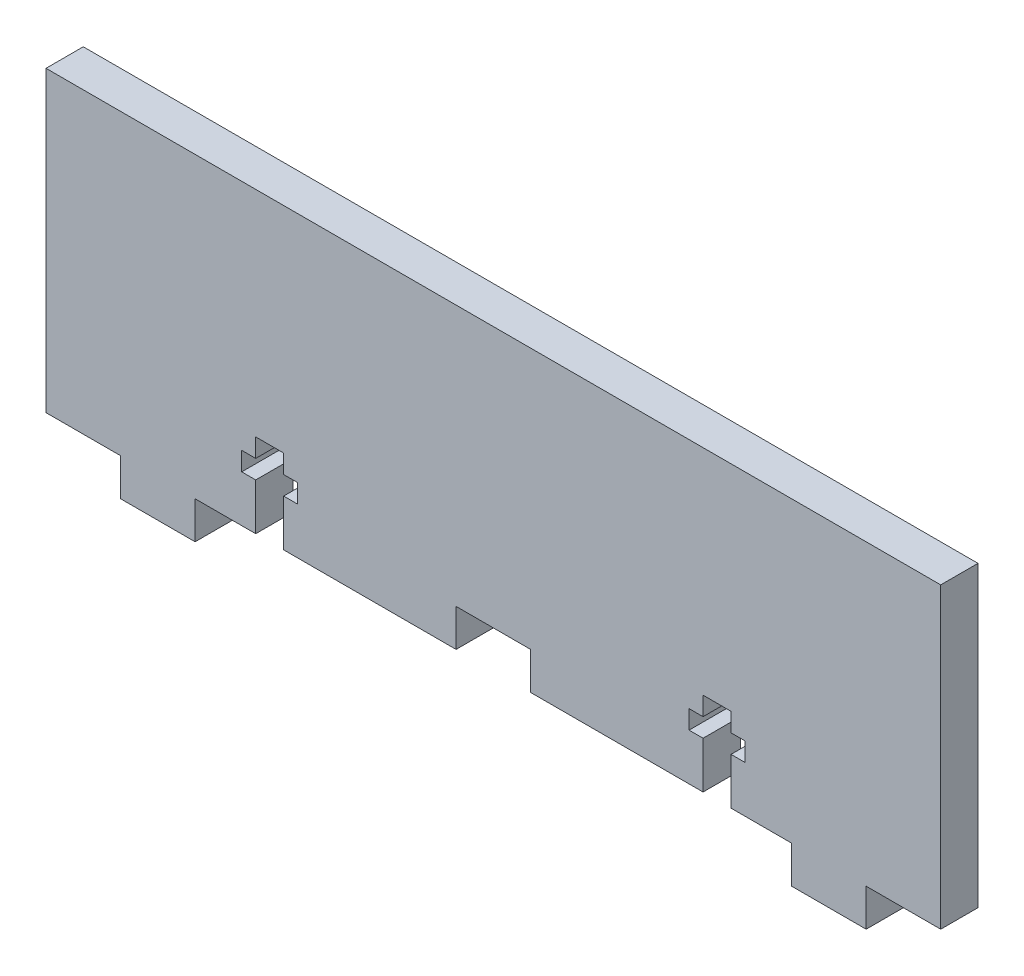
SolidWorks part; units mm, degrees
ref_plane "Front Plane" through (0, 0, 0) normal (0, 0, 1) x (1, 0, 0)
ref_plane "Top Plane" through (0, 0, 0) normal (0, 1, 0) x (1, 0, 0)
ref_plane "Right Plane" through (0, 0, 0) normal (1, 0, 0) x (0, 0, -1)
sketch "Sketch1" plane through (0, 0, 0) normal (0, 0, 1) x (1, 0, 0)
  line L0 (139.7, 6.35) -> (152.4, 6.35)
  line L1 (12.7, 0) -> (25.4, 0)
  line L2 (0, 6.35) -> (0, 57.15)
  line L3 (0, 57.15) -> (152.4, 57.15)
  line L4 (152.4, 6.35) -> (152.4, 57.15)
  line L5 (127, 0) -> (139.7, 0)
  line L6 (0, 6.35) -> (12.7, 6.35)
  line L9 (12.7, 6.35) -> (12.7, 0)
  line L11 (25.4, 0) -> (25.4, 6.35)
  line L12 (25.4, 6.35) -> (127, 6.35)
  line L13 (127, 0) -> (127, 6.35)
  line L17 (139.7, 0) -> (139.7, 6.35)
  dimension "D3" = 12.7
  dimension "D4" = 6.35
  dimension "D5" = 101.6
  dimension "D6" = 12.7
  dimension "D7" = 12.7
extrude "Boss-Extrude1" add sketch "Sketch1" along normal blind 6.35
sketch "Sketch2" plane through (0, 0, 6.35) normal (0, 0, 1) x (1, 0, 0)
  line L0 (111.9188, 6.35) -> (111.9188, 14.2875)
  line L1 (25.4, 6.35) -> (127, 6.35) construction
  line L2 (76.2, 6.35) -> (76.2, 12.7)
  line L3 (25.4, 0) -> (25.4, 6.35) construction
  line L4 (42.8625, 17.4625) -> (42.8625, 14.2875)
  line L5 (40.4813, 6.35) -> (35.7188, 6.35)
  line L6 (82.55, 6.35) -> (69.85, 6.35)
  line L7 (76.2, 6.35) -> (76.2, 12.7)
  line L8 (35.7188, 6.35) -> (35.7188, 14.2875)
  line L9 (82.55, 12.7) -> (69.85, 12.7)
  line L10 (69.85, 6.35) -> (69.85, 12.7)
  line L11 (111.9188, 17.4625) -> (111.9188, 20.6375)
  line L12 (111.9188, 17.4625) -> (109.5375, 17.4625)
  line L13 (111.9188, 14.2875) -> (109.5375, 14.2875)
  line L14 (119.0625, 17.4625) -> (119.0625, 14.2875)
  line L15 (40.4813, 20.6375) -> (35.7188, 20.6375)
  line L16 (35.7188, 17.4625) -> (35.7188, 20.6375)
  line L17 (35.7188, 17.4625) -> (33.3375, 17.4625)
  line L18 (116.6813, 14.2875) -> (119.0625, 14.2875)
  line L19 (35.7188, 14.2875) -> (33.3375, 14.2875)
  line L20 (33.3375, 17.4625) -> (33.3375, 14.2875)
  line L21 (40.4813, 14.2875) -> (42.8625, 14.2875)
  line L22 (116.6813, 17.4625) -> (119.0625, 17.4625)
  line L23 (40.4813, 17.4625) -> (42.8625, 17.4625)
  line L24 (40.4813, 17.4625) -> (40.4813, 20.6375)
  line L25 (116.6813, 17.4625) -> (116.6813, 20.6375)
  line L26 (40.4813, 6.35) -> (40.4813, 14.2875)
  line L27 (111.9188, 20.6375) -> (116.6813, 20.6375)
  line L28 (82.55, 6.35) -> (82.55, 12.7)
  line L29 (116.6813, 6.35) -> (116.6813, 14.2875)
  line L30 (111.9188, 6.35) -> (116.6813, 6.35)
  line L31 (109.5375, 17.4625) -> (109.5375, 14.2875)
  point P6 (25.4, 3.175)
  dimension "D1" = 6.35
  dimension "D2" = 6.35
  dimension "D3" = 2.3813
  dimension "D5" = 7.9375
  dimension "D6" = 3.175
extrude "Cut-Extrude1" cut sketch "Sketch2" against normal blind 6.35 contours L16 L15 L24 L23 L4 L21 L26 L5 L8 L19 L20 L17 | L9 L10 L6 L28 | L11 L27 L25 L22 L14 L18 L29 L30 L0 L13 L31 L12
